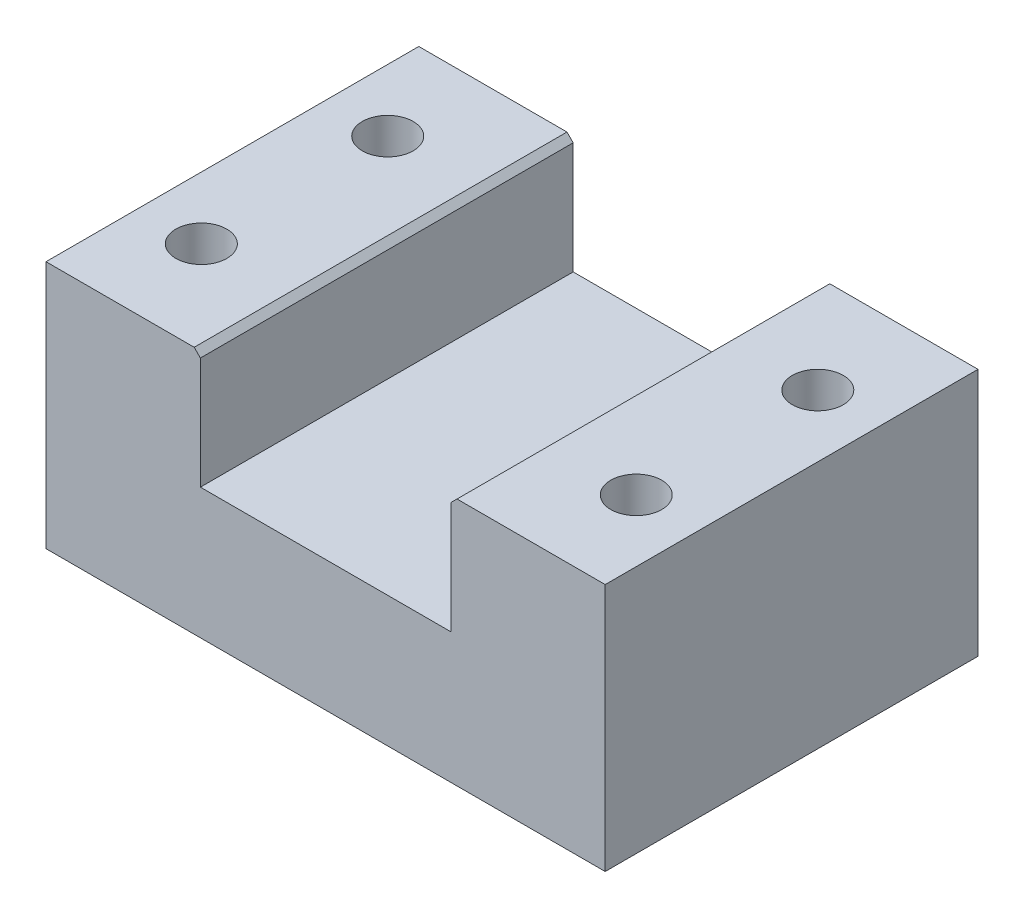
SolidWorks part; units mm, degrees
ref_plane "Спереди" through (0, 0, 0) normal (0, 0, 1) x (1, 0, 0)
ref_plane "Сверху" through (0, 0, 0) normal (0, 1, 0) x (1, 0, 0)
ref_plane "Справа" through (0, 0, 0) normal (1, 0, 0) x (0, 0, -1)
sketch "Sketch1" plane through (0, 0, 0) normal (0, 1, 0) x (1, 0, 0)
  line L1 (45, -30) -> (-45, -30)
  line L2 (45, -30) -> (45, 30)
  line L3 (45, 30) -> (-45, 30)
  line L4 (-45, -30) -> (-45, 30)
  line L5 (45, -30) -> (-45, 30) construction
  line L6 (45, 30) -> (-45, -30) construction
  point P0 (0, 0)
  dimension "D1" = 90
  dimension "D2" = 60
extrude "Boss-Extrude1" add sketch "Sketch1" along normal blind 40
sketch "Sketch2" plane through (0, 0, 30) normal (0, 0, 1) x (1, 0, 0)
  line L0 (-45, 40) -> (45, 40) construction
  line L1 (20.15, 59) -> (-20.15, 59)
  line L2 (20.15, 59) -> (20.15, 21)
  line L3 (20.15, 21) -> (-20.15, 21)
  line L4 (-20.15, 59) -> (-20.15, 21)
  line L5 (20.15, 59) -> (-20.15, 21) construction
  line L6 (20.15, 21) -> (-20.15, 59) construction
  point P0 (0, 40)
  dimension "D1" = 40.3
  dimension "D2" = 38
extrude "Cut-Extrude1" cut sketch "Sketch2" against normal through all
sketch "Sketch3" plane through (0, 0, 0) normal (0, -1, 0) x (1, 0, 0)
  line L1 (-35, -15) -> (35, -15) construction
  line L2 (-35, -15) -> (-35, 15) construction
  line L3 (-35, 15) -> (35, 15) construction
  line L4 (35, -15) -> (35, 15) construction
  line L5 (-35, -15) -> (35, 15) construction
  line L6 (-35, 15) -> (35, -15) construction
  circle A0 centre (-35, 15) radius 4.1
  circle A1 centre (-35, -15) radius 4.1
  circle A2 centre (35, -14.2173) radius 4.1
  circle A3 centre (35, 15) radius 4.1
  point P0 (0, 0)
  dimension "D3" = 8.2
  dimension "D1" = 30
  dimension "D2" = 70
extrude "Cut-Extrude2" cut sketch "Sketch3" against normal through all
chamfer "Chamfer1" distance 1 angle 45 2 edges at (20.15, 40, 0) (-20.15, 40, 0)
